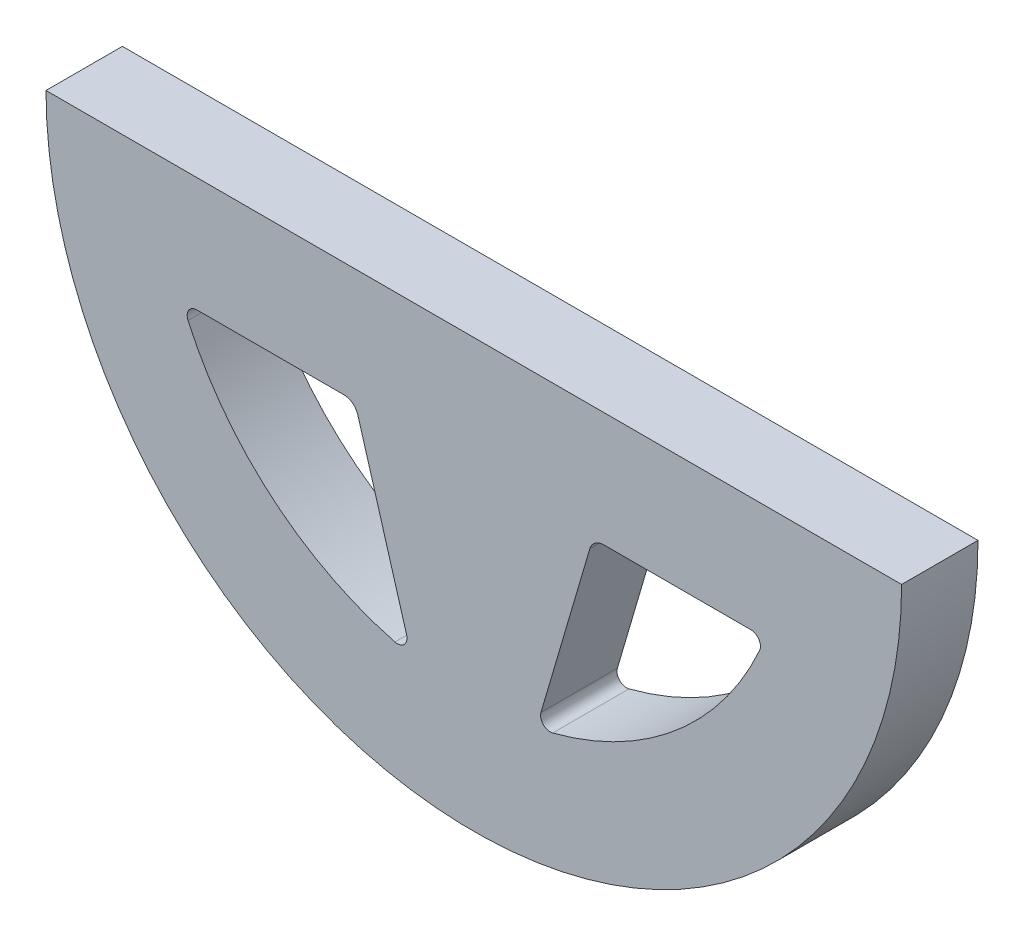
SolidWorks part; units mm, degrees
ref_plane "Front Plane" through (0, 0, 0) normal (0, 0, 1) x (1, 0, 0)
ref_plane "Top Plane" through (0, 0, 0) normal (0, 1, 0) x (1, 0, 0)
ref_plane "Right Plane" through (0, 0, 0) normal (1, 0, 0) x (0, 0, -1)
sketch "Sketch1" plane through (0, 0, 0) normal (0, 0, 1) x (1, 0, 0)
  line L0 (-3.175, 0) -> (-3.175, -17.78) construction
  line L1 (-20.955, 0) -> (14.605, 0)
  line L2 (1.7743, -4.7625) -> (8.94, -4.7625)
  line L3 (-15.29, -4.7625) -> (-8.1243, -4.7625)
  line L6 (-8.1243, -4.7625) -> (-5.7734, -12.7555)
  line L7 (1.7743, -4.7625) -> (-0.5766, -12.7555)
  line L11 (-15.29, -4.7625) -> (-3.175, -4.7625) construction
  line L12 (-20.955, 0) -> (-3.175, 0) construction
  line L13 (3.175, 0) -> (14.605, 0) construction
  line L14 (3.175, -4.7625) -> (8.94, -4.7625) construction
  arc A1 (-20.955, 0) -> (14.605, 0) centre (-3.175, 0) ccw
  arc A2 (-15.29, -4.7625) -> (-5.7734, -12.7555) centre (-3.175, 0) ccw
  arc A3 (-0.5766, -12.7555) -> (8.94, -4.7625) centre (-3.175, 0) ccw
  arc A5 (-15.29, -4.7625) -> (8.94, -4.7625) centre (-3.175, 0) ccw construction
  point P12 (-3.175, 0)
  dimension "D1" = 4.7625
  dimension "D3" = 17.78
extrude "Boss-Extrude1" add sketch "Sketch1" along normal blind 3.175
fillet "Fillet1" radius 0.4 4 edges at (8.94, -4.7625, 1.5875) (-0.5766, -12.7555, 1.5875) (-5.7734, -12.7555, 1.5875) (-15.29, -4.7625, 1.5875)
fillet "Fillet2" radius 0.6 2 edges at (1.7743, -4.7625, 1.5875) (-8.1243, -4.7625, 1.5875)
